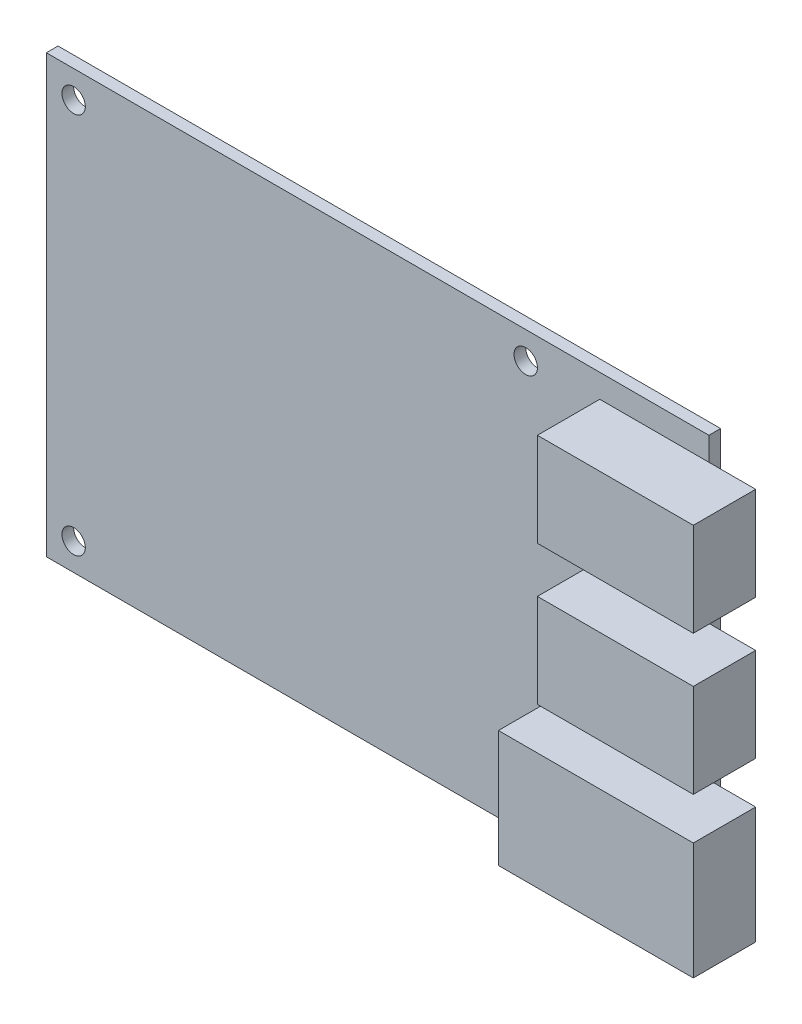
SolidWorks part; units mm, degrees
ref_plane "Front Plane" through (0, 0, 0) normal (0, 0, 1) x (1, 0, 0)
ref_plane "Top Plane" through (0, 0, 0) normal (0, 1, 0) x (1, 0, 0)
ref_plane "Right Plane" through (0, 0, 0) normal (1, 0, 0) x (0, 0, -1)
sketch "Sketch1" plane through (0, 0, 0) normal (0, 0, 1) x (1, 0, 0)
  line L1 (42.5, -28) -> (-42.5, -28)
  line L2 (42.5, -28) -> (42.5, 28)
  line L3 (42.5, 28) -> (-42.5, 28)
  line L4 (-42.5, -28) -> (-42.5, 28)
  line L5 (42.5, -28) -> (-42.5, 28) construction
  line L6 (42.5, 28) -> (-42.5, -28) construction
  line L11 (-39, 24.5) -> (19, 24.5) construction
  line L12 (-39, 24.5) -> (-39, -24.5) construction
  line L13 (-39, -24.5) -> (19, -24.5) construction
  line L14 (19, 24.5) -> (19, -24.5) construction
  circle A0 centre (-39, 24.5) radius 1.5
  circle A1 centre (19, 24.5) radius 1.5
  circle A2 centre (19, -24.5) radius 1.5
  circle A3 centre (-39, -24.5) radius 1.5
  point P0 (0, 0)
  point P6 (0, 0)
  point P11 (-42.5, 0)
  point P12 (-39, 0)
  dimension "D6" = 3
  dimension "D1" = 85
  dimension "D2" = 56
  dimension "D3" = 3.5
  dimension "D4" = 58
  dimension "D5" = 49
extrude "Boss-Extrude1" add sketch "Sketch1" along normal blind 1.5
sketch "Sketch2" plane through (0, 0, 1.5) normal (0, 0, 1) x (1, 0, 0)
  line L0 (-42.5, -28) -> (42.5, -28) construction
  line L1 (23.5, -25.3) -> (48.5, -25.3)
  line L2 (23.5, -25.3) -> (23.5, -10.3)
  line L3 (23.5, -10.3) -> (48.5, -10.3)
  line L4 (48.5, -25.3) -> (48.5, -10.3)
  line L5 (28.5, -4.9) -> (48.5, -4.9)
  line L6 (28.5, -4.9) -> (28.5, 7.1)
  line L7 (28.5, 7.1) -> (48.5, 7.1)
  line L8 (48.5, -4.9) -> (48.5, 7.1)
  line L9 (28.5, 13) -> (48.5, 13)
  line L10 (28.5, 13) -> (28.5, 25)
  line L11 (28.5, 25) -> (48.5, 25)
  line L12 (48.5, 13) -> (48.5, 25)
  line L13 (42.5, -28) -> (42.5, 28) construction
  point P13 (48.5, -17.8)
  point P16 (48.5, 1.1)
  point P17 (48.5, 19)
  point P19 (53.8937, 11.2535)
  dimension "D1" = 10.2
  dimension "D2" = 29.1
  dimension "D3" = 47
  dimension "D4" = 6
  dimension "D5" = 12
  dimension "D6" = 20
  dimension "D7" = 25
  dimension "D8" = 15
extrude "Boss-Extrude2" add sketch "Sketch2" along normal blind 8
